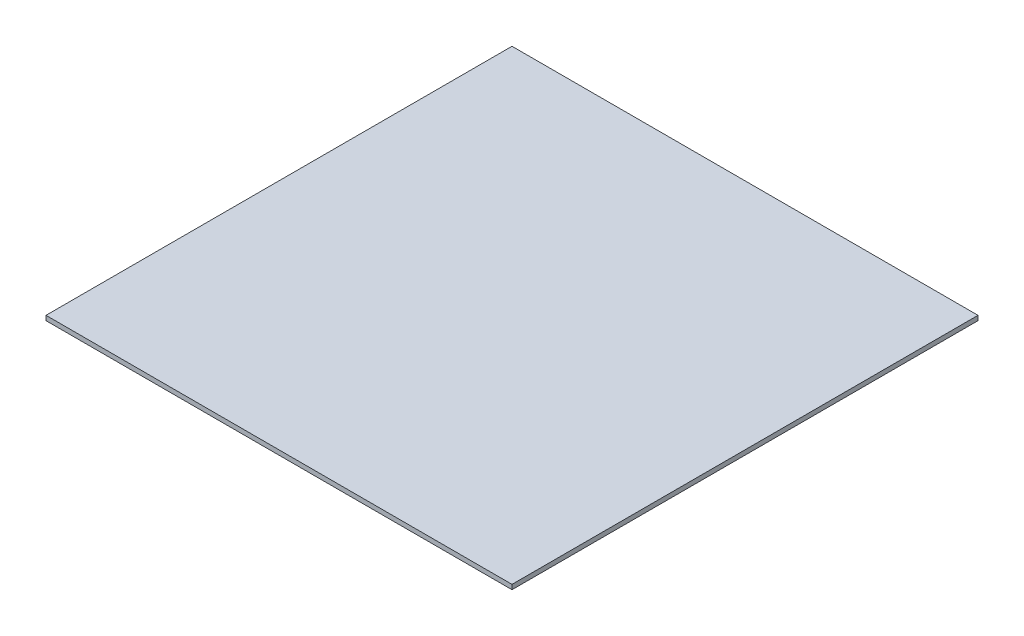
SolidWorks part; units mm, degrees
ref_plane "Front Plane" through (0, 0, 0) normal (0, 0, 1) x (1, 0, 0)
ref_plane "Top Plane" through (0, 0, 0) normal (0, 1, 0) x (1, 0, 0)
ref_plane "Right Plane" through (0, 0, 0) normal (1, 0, 0) x (0, 0, -1)
sketch "Sketch1" plane through (0, 0, 0) normal (0, 1, 0) x (1, 0, 0)
  line L1 (250, -250) -> (-250, -250)
  line L2 (250, -250) -> (250, 250)
  line L3 (250, 250) -> (-250, 250)
  line L4 (-250, -250) -> (-250, 250)
  line L5 (250, -250) -> (-250, 250) construction
  line L6 (250, 250) -> (-250, -250) construction
  circle A0 centre (250, 150) radius 90
  point P0 (0, 0)
  dimension "D5" = 180
  dimension "D1" = 500
  dimension "D2" = 500
  dimension "D3" = 250
  dimension "D4" = 150
extrude "Boss-Extrude1" add sketch "Sketch1" against normal blind 5 contours L2 L3 L4 L1
sketch "Sketch2" plane through (0, 0, 0) normal (0, 1, 0) x (1, 0, 0)
  line L4 (-250, -250) -> (250, -250)
  line L5 (-250, 250) -> (-250, -250)
  line L6 (250, 250) -> (-250, 250)
  line L7 (250, -250) -> (250, 250)
  line L11 (250, 60) -> (250, 250)
  circle A1 centre (250, 150) radius 90
  arc A2 (250, 240) -> (250, 60) centre (250, 150) ccw
  point P4 (160, 150)
  point P9 (160.6562, 160.8483)
  point P10 (281.9144, 65.8485)
  point P11 (291.8251, 70.309)
  point P12 (162.6152, 171.5384)
  point P13 (165.8485, 181.9144)
  point P14 (170.309, 191.8251)
  point P15 (175.9315, 201.1258)
  point P16 (182.634, 209.681)
  point P17 (190.319, 217.366)
  point P18 (198.8742, 224.0685)
  point P19 (208.1749, 229.691)
  point P20 (218.0856, 234.1515)
  point P21 (228.4616, 237.3848)
  point P22 (239.1517, 239.3438)
  point P23 (250, 240)
  point P24 (260.8483, 60.6562)
  point P25 (260.8483, 239.3438)
  point P26 (271.5384, 237.3848)
  point P27 (281.9144, 234.1515)
  point P28 (291.8251, 229.691)
  point P29 (301.1258, 224.0685)
  point P30 (309.681, 217.366)
  point P31 (317.366, 209.681)
  point P32 (324.0685, 201.1258)
  point P33 (329.691, 191.8251)
  point P34 (334.1515, 181.9144)
  point P35 (337.3848, 171.5384)
  point P36 (339.3438, 160.8483)
  point P37 (340, 150)
  point P38 (339.3438, 139.1517)
  point P39 (337.3848, 128.4616)
  point P40 (334.1515, 118.0856)
  point P41 (329.691, 108.1749)
  point P42 (324.0685, 98.8742)
  point P43 (317.366, 90.319)
  point P44 (309.681, 82.634)
  point P45 (301.1258, 75.9315)
  point P46 (271.5384, 62.6152)
  point P49 (250, 60)
  point P50 (239.1517, 60.6562)
  point P51 (228.4616, 62.6152)
  point P52 (218.0856, 65.8485)
  point P53 (208.1749, 70.309)
  point P54 (198.8742, 75.9315)
  point P55 (190.319, 82.634)
  point P56 (182.634, 90.319)
  point P57 (175.9315, 98.8742)
  point P58 (170.309, 108.1749)
  point P59 (165.8485, 118.0856)
  point P60 (162.6152, 128.4616)
  point P61 (160.6562, 139.1517)
  point P62 (209.5165, 114.8749)
  dimension "D4" = 250
  dimension "D5" = 150
  dimension "D1" = 0
  dimension "D2" = 0
  dimension "D3" = 52
sketch "Sketch3" plane through (0, 0, 0) normal (0, 1, 0) x (1, 0, 0)
  point P0 (0, 0)
